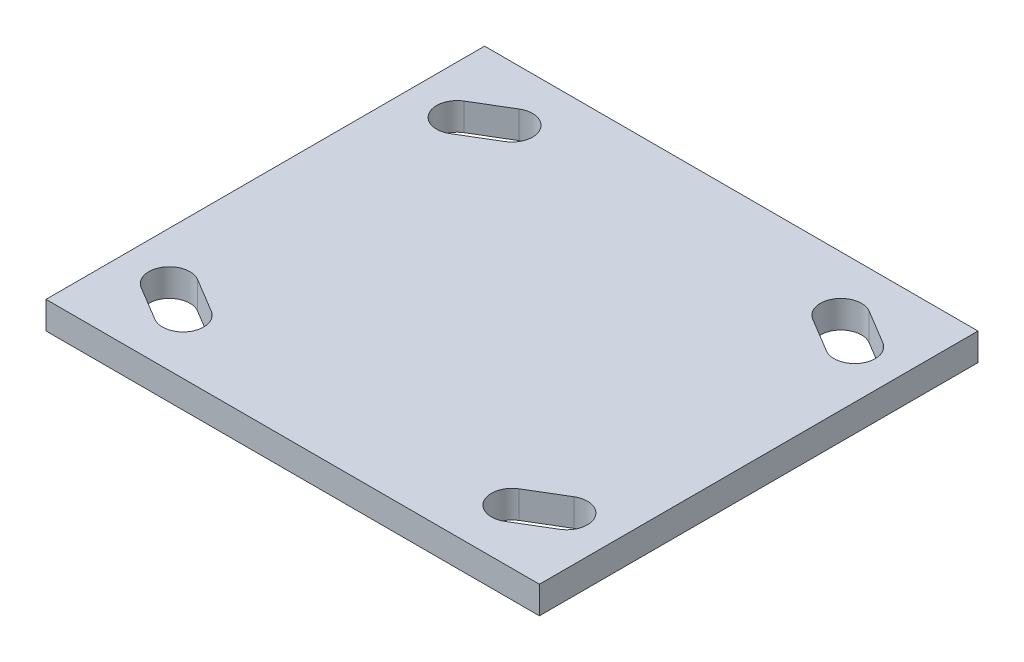
SolidWorks part; units mm, degrees
material "6061 Alloy"
ref_plane "Front Plane" through (0, 0, 0) normal (0, 0, 1) x (1, 0, 0)
ref_plane "Top Plane" through (0, 0, 0) normal (0, 1, 0) x (1, 0, 0)
ref_plane "Right Plane" through (0, 0, 0) normal (1, 0, 0) x (0, 0, -1)
sketch "Sketch1" plane through (0, 0, 0) normal (0, 0, 1) x (1, 0, 0)
  line L1 (-57.15, 0) -> (57.15, 0)
  line L2 (-57.15, 0) -> (-57.15, -6.35)
  line L3 (-57.15, -6.35) -> (57.15, -6.35)
  line L4 (57.15, 0) -> (57.15, -6.35)
  dimension "Plate Length" = 114.3
  dimension "Plate Thickness" = 6.35
extrude "Boss-Extrude1" add sketch "Sketch1" along normal mid plane 101.6
sketch "Sketch2" plane through (0, 0, 0) normal (0, 1, 0) x (1, 0, 0)
  line L0 (-38.1, 38.1) -> (-46.0375, 33.3375) construction
  line L1 (-35.6497, 34.0162) -> (-43.5872, 29.2537)
  line L2 (-40.5503, 42.1838) -> (-48.4878, 37.4213)
  line L3 (0, 0) -> (0, 50.8) construction
  line L4 (0, 0) -> (57.15, 0) construction
  line L5 (57.15, -50.8) -> (57.15, 50.8) construction
  line L6 (57.15, 50.8) -> (-57.15, 50.8) construction
  line L7 (-38.1, -38.1) -> (-46.0375, -33.3375) construction
  line L8 (-35.6497, -34.0162) -> (-43.5872, -29.2537)
  line L9 (-40.5503, -42.1838) -> (-48.4878, -37.4213)
  line L10 (38.1, 38.1) -> (46.0375, 33.3375) construction
  line L11 (35.6497, 34.0162) -> (43.5872, 29.2537)
  line L12 (40.5503, 42.1838) -> (48.4878, 37.4213)
  line L13 (38.1, -38.1) -> (46.0375, -33.3375) construction
  line L14 (35.6497, -34.0162) -> (43.5872, -29.2537)
  line L15 (40.5503, -42.1838) -> (48.4878, -37.4213)
  arc A0 (-35.6497, 34.0162) -> (-40.5503, 42.1838) centre (-38.1, 38.1) ccw
  arc A1 (-48.4878, 37.4213) -> (-43.5872, 29.2537) centre (-46.0375, 33.3375) ccw
  arc A2 (-35.6497, -34.0162) -> (-40.5503, -42.1838) centre (-38.1, -38.1) cw
  arc A3 (-48.4878, -37.4213) -> (-43.5872, -29.2537) centre (-46.0375, -33.3375) cw
  arc A4 (35.6497, 34.0162) -> (40.5503, 42.1838) centre (38.1, 38.1) cw
  arc A5 (48.4878, 37.4213) -> (43.5872, 29.2537) centre (46.0375, 33.3375) cw
  arc A6 (35.6497, -34.0162) -> (40.5503, -42.1838) centre (38.1, -38.1) ccw
  arc A7 (48.4878, -37.4213) -> (43.5872, -29.2537) centre (46.0375, -33.3375) ccw
  point P2 (-42.0687, 35.7188)
  point P17 (-42.0687, -35.7188)
  point P24 (42.0688, 35.7188)
  point P31 (42.0687, -35.7187)
  dimension "D3" = 92.075
  dimension "D5" = 76.2
  dimension "D1" = 9.525
  dimension "D2" = 76.2
  dimension "D4" = 66.675
extrude "1-2 holes" cut sketch "Sketch2" against normal through all
sketch "Sketch3" plane through (0, 0, 0) normal (0, 1, 0) x (1, 0, 0)
  line L0 (0, 0) -> (0, 50.8) construction
  line L1 (57.15, 50.8) -> (-57.15, 50.8) construction
  line L2 (0, 0) -> (57.15, 0) construction
  line L3 (57.15, -50.8) -> (57.15, 50.8) construction
  circle A0 centre (-57.15, 52.3875) radius 4.7625
  circle A1 centre (57.15, 52.3875) radius 4.7625
  circle A2 centre (57.15, -52.3875) radius 4.7625
  circle A3 centre (-57.15, -52.3875) radius 4.7625
  dimension "D1" = 9.525
  dimension "D2" = 114.3
  dimension "D3" = 104.775
extrude "3-holes" [suppressed] cut sketch "Sketch3" against normal through all
